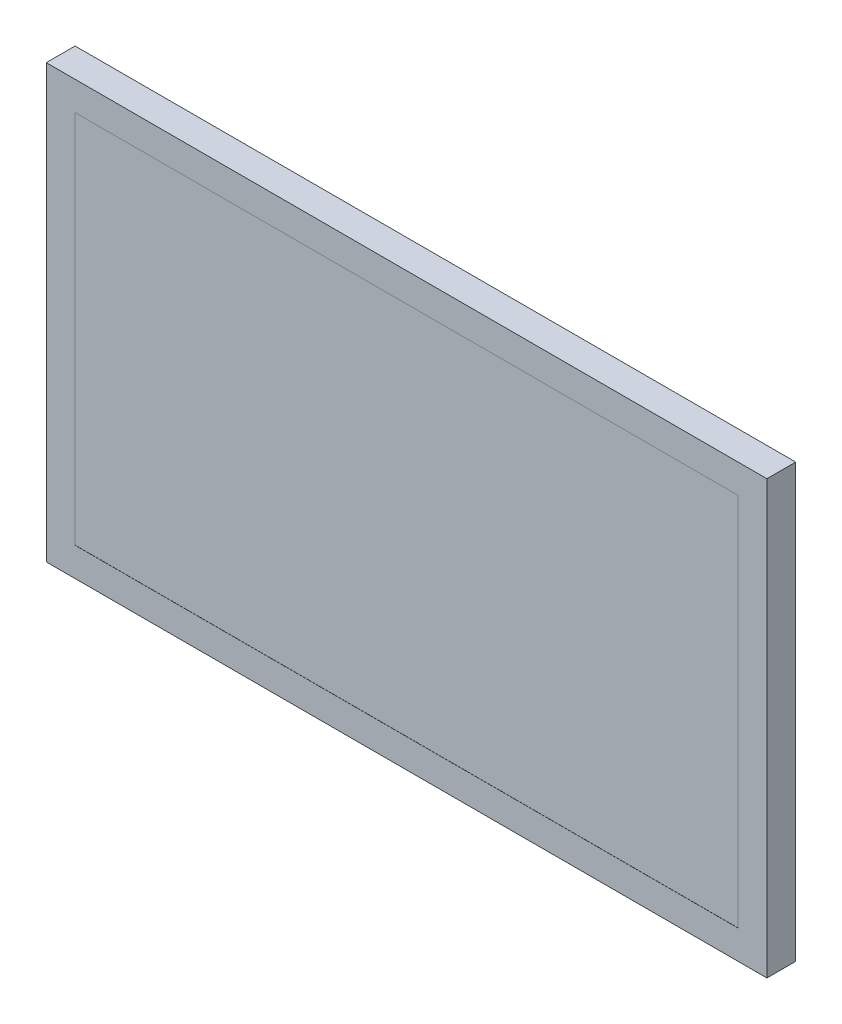
SolidWorks part; units mm, degrees
ref_plane "Front Plane" through (0, 0, 0) normal (0, 0, 1) x (1, 0, 0)
ref_plane "Top Plane" through (0, 0, 0) normal (0, 1, 0) x (1, 0, 0)
ref_plane "Right Plane" through (0, 0, 0) normal (1, 0, 0) x (0, 0, -1)
sketch "Sketch1" plane through (0, 0, 0) normal (0, 0, 1) x (1, 0, 0)
  line L1 (250, -150) -> (-250, -150)
  line L2 (250, -150) -> (250, 150)
  line L3 (250, 150) -> (-250, 150)
  line L4 (-250, -150) -> (-250, 150)
  line L5 (250, -150) -> (-250, 150) construction
  line L6 (250, 150) -> (-250, -150) construction
  point P0 (0, 0)
  dimension "D1" = 500
  dimension "D2" = 300
extrude "Boss-Extrude1" add sketch "Sketch1" along normal blind 20
sketch "Sketch2" plane through (0, 0, 20) normal (0, 0, 1) x (1, 0, 0)
  line L0 (250, 150) -> (-250, 150) construction
  line L1 (230, -130) -> (-230, -130)
  line L2 (230, -130) -> (230, 130)
  line L3 (230, 130) -> (-230, 130)
  line L4 (-230, -130) -> (-230, 130)
  line L5 (230, -130) -> (-230, 130) construction
  line L6 (230, 130) -> (-230, -130) construction
  line L7 (-250, 150) -> (-250, -150) construction
  point P0 (0, 0)
  dimension "D1" = 20
  dimension "D2" = 20
extrude "Cut-Extrude1" cut sketch "Sketch2" against normal blind 0.1
